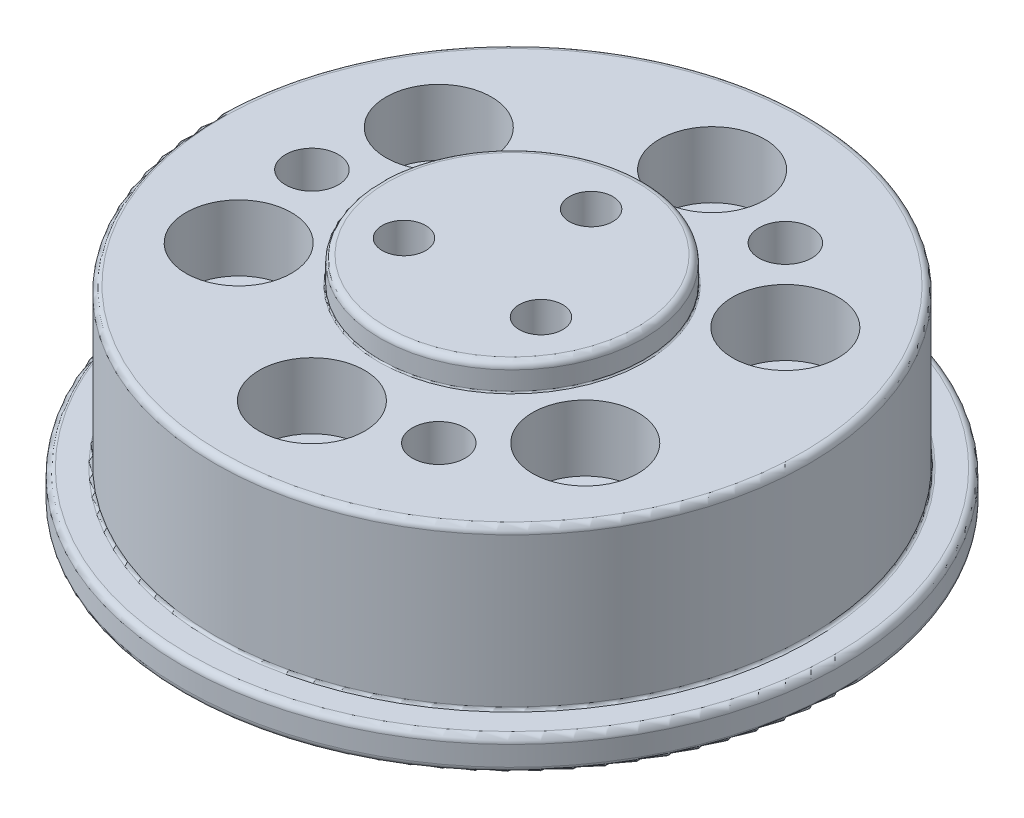
SolidWorks part; units mm, degrees
material "7075-T6, 플레이트 (SS)"
ref_plane "정면" through (0, 0, 0) normal (0, 0, 1) x (1, 0, 0)
ref_plane "윗면" through (0, 0, 0) normal (0, 1, 0) x (1, 0, 0)
ref_plane "우측면" through (0, 0, 0) normal (1, 0, 0) x (0, 0, -1)
sketch "스케치1" plane through (0, 0, 0) normal (0, 1, 0) x (1, 0, 0)
  circle A0 centre (0, 0) radius 10.1
  dimension "D1" = 20.2
extrude "보스-돌출1" add sketch "스케치1" along normal blind 2.5
sketch "스케치2" plane through (0, 2.5, 0) normal (0, 1, 0) x (1, 0, 0)
  circle A0 centre (0, 0) radius 25
  dimension "D1" = 50
extrude "보스-돌출2" add sketch "스케치2" along normal blind 2.5
sketch "스케치3" plane through (0, 5, 0) normal (0, 1, 0) x (1, 0, 0)
  circle A0 centre (0, 0) radius 22.5
  dimension "D1" = 45
extrude "보스-돌출4" add sketch "스케치3" along normal blind 12 contours A0
sketch "스케치5" plane through (0, 17, 0) normal (0, 1, 0) x (1, 0, 0)
  circle A0 centre (0, 0) radius 10
  circle A1 centre (0, 0) radius 22.5 construction
  dimension "D1" = 20
extrude "보스-돌출5" add sketch "스케치5" along normal blind 2
sketch "스케치6" plane through (0, 17, 0) normal (0, 1, 0) x (1, 0, 0)
  circle A0 centre (0, 0) radius 15.18 construction
  point P3 (0, 15.18)
  dimension "D1" = 30.36
hole_wizard "M4 육각 소켓 머리 캡 나사용 카운터보어1" positions "스케치7" profile "스케치8" counterbore size "M4" standard "ISO" end condition through all
sketch "스케치7" plane through (0, 17, 0) normal (0, 1, 0) x (1, 0, 0)
  point P0 (0, 15.18)
sketch "스케치8" plane through (0, 17, -15.18) normal (1, 0, 0) x (0, 0, 1)
  line L0 (0, 0) -> (0, 17)
  line L1 (0, 17) -> (2.25, 17)
  line L3 (2.25, 17) -> (2.25, 5)
  line L4 (2.25, 5) -> (4, 5)
  line L5 (4, 5) -> (4, 0)
  line L7 (4, 0) -> (0, 0)
  line L11 (0, -6.35) -> (0, 107.95) construction
  dimension "관통 구멍 지름" = 4.5
  dimension "관통 구멍 깊이" = 17
  dimension "카운터보어 지름" = 8
  dimension "카운터보어 깊이" = 5
pattern_circular "원형 패턴1" count 6 over 360 about axis through (0, 0, 0) along (0, 1, 0) of "M4 육각 소켓 머리 캡 나사용 카운터보어1"
sketch "스케치11" plane through (0, 19, 0) normal (0, 1, 0) x (1, 0, 0)
  circle A0 centre (0, 0) radius 6 construction
  point P3 (0, 6)
  dimension "D1" = 12
hole_wizard "M4 탭을 위한 탭 드릴1" positions "스케치12" profile "스케치13" hole size "M4" standard "ISO"
sketch "스케치12" plane through (0, 19, 0) normal (0, 1, 0) x (1, 0, 0)
  point P0 (0, 6)
sketch "스케치13" plane through (0, 19, -6) normal (1, 0, 0) x (0, 0, 1)
  line L0 (0, 0) -> (0, 5.9914)
  line L1 (0, 5.9914) -> (1.65, 5)
  line L2 (1.65, 5) -> (1.65, 0)
  line L5 (1.65, 0) -> (0, 0)
  line L10 (0, 5.9914) -> (-1.65, 5) construction
  line L11 (0, -6.35) -> (0, 107.95) construction
  dimension "구멍 지름" = 3.3
  dimension "구멍 깊이" = 5
  dimension "드릴 각도" = 118
pattern_circular "원형 패턴2" count 3 over 360 about axis through (0, 0, 0) along (0, 1, 0) of "M4 탭을 위한 탭 드릴1"
fillet "필렛1" radius 0.5 5 edges at (0, 0, 10.1) (0, 2.5, 10.1) (0, 2.5, 25) (0, 5, 25) (0, 17, 22.5)
fillet "필렛2" radius 0.2 1 edges at (0, 5, 22.5)
fillet "필렛3" radius 0.1 1 edges at (0, 17, 10)
fillet "필렛4" radius 0.5 1 edges at (0, 19, 10)
sketch "스케치14" plane through (0, 17, 0) normal (0, 1, 0) x (1, 0, 0)
  circle A3 centre (0, 0) radius 15.18 construction
  point P3 (-15.18, 0)
  point P4 (0, 0)
hole_wizard "Ø4.0mm 맞춤핀 구멍1" positions "스케치15" profile "스케치17" hole size "Ø4.0" standard "ISO" end condition through all
sketch "스케치15" plane through (0, 17, 0) normal (0, 1, 0) x (1, 0, 0)
  point P0 (-15.18, 0)
sketch "스케치17" plane through (-15.18, 17, 0) normal (1, 0, 0) x (0, 0, 1)
  line L0 (0, 0) -> (0, 17)
  line L1 (0, 17) -> (2, 17)
  line L2 (2, 17) -> (2, 0)
  line L5 (2, 0) -> (0, 0)
  line L11 (0, -6.35) -> (0, 107.95) construction
  dimension "관통 구멍 지름" = 4
  dimension "관통 구멍 깊이" = 17
pattern_circular "원형 패턴3" count 3 over 360 about axis through (0, 0, 0) along (0, 1, 0) of "Ø4.0mm 맞춤핀 구멍1"
